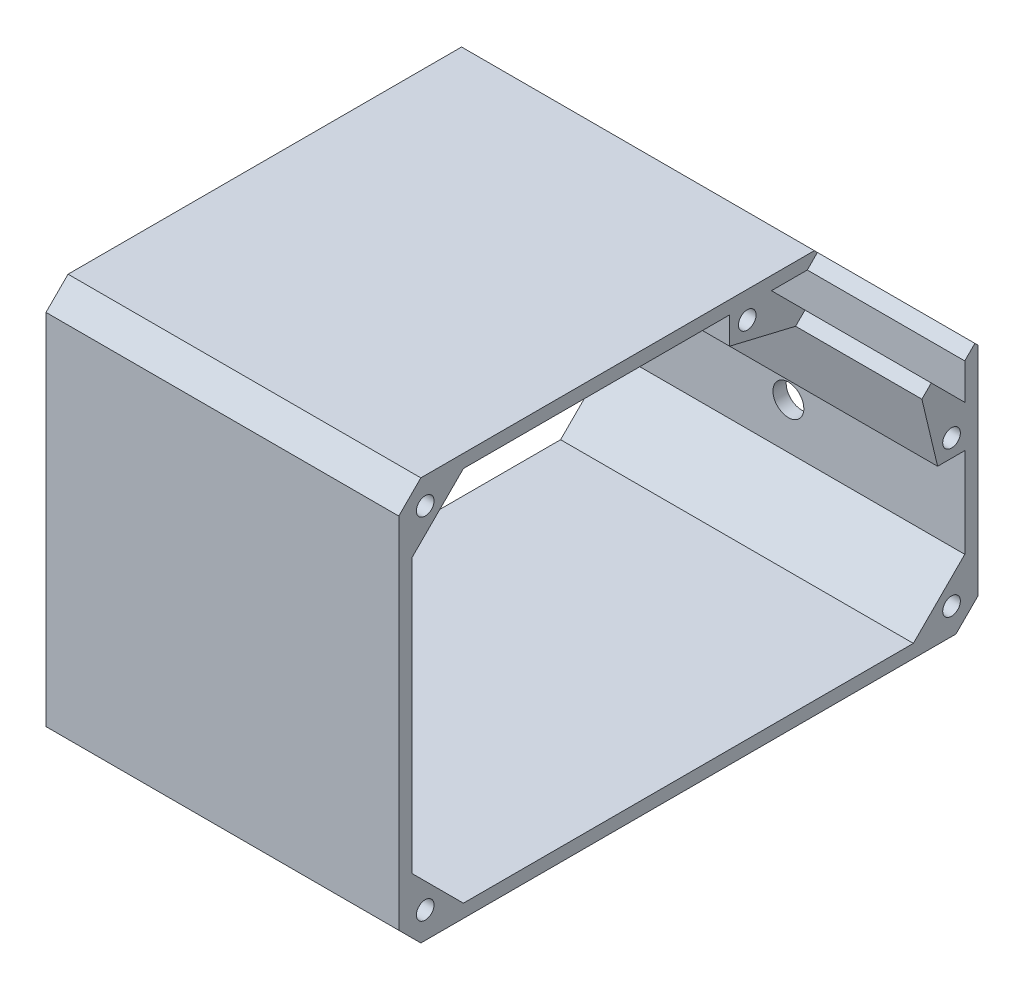
SolidWorks part; units mm, degrees
ref_plane "Front Plane" through (0, 0, 0) normal (0, 0, 1) x (1, 0, 0)
ref_plane "Top Plane" through (0, 0, 0) normal (0, 1, 0) x (1, 0, 0)
ref_plane "Right Plane" through (0, 0, 0) normal (1, 0, 0) x (0, 0, -1)
sketch "Sketch2" plane through (0, 0, 0) normal (1, 0, 0) x (0, 0, -1)
  line L1 (53.7307, 35.7377) -> (89.086, 0.3824) construction
  line L3 (89.086, -49.6176) -> (-36.2693, -49.6176)
  line L4 (-36.2693, -49.6176) -> (-36.2693, 35.7377)
  line L5 (-39.2693, -52.6176) -> (-39.2693, 38.7377)
  line L6 (-39.2693, 38.7377) -> (54.9733, 38.7377)
  line L7 (54.9733, 38.7377) -> (92.086, 1.625) construction
  line L8 (92.086, 1.625) -> (92.086, -52.6176)
  line L9 (92.086, -52.6176) -> (-39.2693, -52.6176)
  line L10 (53.7307, 35.7377) -> (55.852, 37.859) construction
  line L11 (89.086, 0.3824) -> (91.2073, 2.5037) construction
  line L12 (49.3113, 31.6718) -> (89.086, -8.1029) construction
  line L13 (53.3771, 35.7377) -> (55.6752, 38.0358)
  line L14 (55.6752, 38.0358) -> (54.9733, 38.7377)
  line L15 (91.2073, 2.5037) -> (92.086, 1.625)
  line L16 (89.086, 0.0288) -> (91.3841, 2.3269)
  line L17 (85.1969, -8.4565) -> (44.8918, 31.8486) construction
  line L18 (-36.2693, 35.7377) -> (53.3771, 35.7377)
  line L19 (-36.2693, 35.7377) -> (53.7307, 35.7377) construction
  line L20 (89.086, -49.6176) -> (89.086, 0.0288)
  line L21 (89.086, 0.3824) -> (89.086, -49.6176) construction
  line L22 (44.8918, 31.8486) -> (50.7255, 26.015)
  line L23 (50.7255, 26.015) -> (52.8468, 28.1363)
  line L24 (52.8468, 28.1363) -> (49.3113, 31.6718)
  line L25 (53.3771, 35.7377) -> (49.3113, 31.6718)
  line L26 (85.1969, -8.4565) -> (79.363, -2.6225)
  line L27 (79.363, -2.6225) -> (81.4843, -0.5012)
  line L28 (85.0198, -4.0367) -> (81.4843, -0.5012)
  line L29 (89.086, -8.1029) -> (89.086, 0.0288)
  line L30 (89.086, 0.0288) -> (85.0198, -4.0367)
  line L31 (49.3113, 31.6718) -> (45.2454, 35.7377)
  line L32 (44.8918, 31.8486) -> (51.0028, 35.7377)
  line L33 (85.1969, -8.4565) -> (89.086, -12.3456)
  line L34 (85.0198, -4.0367) -> (89.086, -8.1029)
  line L35 (-36.2693, 24.0809) -> (-24.6125, 35.7377)
  line L36 (50.7255, 26.015) -> (9.8915, 35.7377) construction
  line L37 (35.7601, 35.7377) -> (35.7601, 29.5783)
  line L38 (35.7601, 29.5783) -> (50.7255, 26.015)
  line L39 (-36.2693, -37.9608) -> (-24.6125, -49.6176)
  line L40 (73.5297, 20.1814) -> (65.0444, 11.6961) construction
  line L41 (89.086, -17.5882) -> (82.9266, -17.5882)
  line L42 (82.9266, -17.5882) -> (79.3633, -2.6228)
  line L43 (26.4084, -52.6176) -> (26.4084, 38.7377) construction
  line L44 (89.086, -37.9608) -> (77.4292, -49.6176)
  circle A0 centre (-33.2693, 32.7377) radius 2
  circle A1 centre (39.7601, 32.7377) radius 2
  circle A2 centre (-33.2693, -46.6176) radius 2
  circle A4 centre (86.086, -13.5882) radius 2
  circle A5 centre (86.086, -46.6176) radius 2
  dimension "D11" = 4
  dimension "D14" = 4
  dimension "D16" = 4
  dimension "D19" = 4
  dimension "D21" = 4
  dimension "D25" = 4
  dimension "D1" = 90
  dimension "D2" = 5
  dimension "D3" = 50
  dimension "D4" = 50
  dimension "D6" = 6
  dimension "D7" = 0.25
  dimension "D8" = 0.25
  dimension "D9" = 3
  dimension "D10" = 5
  dimension "D12" = 6
  dimension "D13" = 6
  dimension "D15" = 135
  dimension "D17" = 6
  dimension "D18" = 6
  dimension "D20" = 4
  dimension "D22" = 135
  dimension "D23" = 6
  dimension "D24" = 6
  dimension "D5" = 3
extrude "Boss-Extrude2" add sketch "Sketch2" along normal blind 80 contours L20 L3 L4 L18 L13 L14 L6 L5 L9 L8 L15 L16 | L4 L35 L18 A0 | L37 L38 L22 L32 L18 A1 | L32 L22 L23 L24 L31 L18 | L42 L41 L20 L33 L26 A4 | L34 L28 L27 L26 L33 L20 | L20 L44 L3 A5 | L39 L4 L3 A2
chamfer "Chamfer2" distance 5 angle 45 3 edges at (40, -52.6176, -92.086) (40, -52.6176, 39.2693) (40, 38.7377, 39.2693)
sketch "Sketch3" plane through (0, 0, -92.086) normal (0, 0, -1) x (-1, 0, 0)
  line L0 (-40, -47.6176) -> (-40, 1.625) construction
  line L1 (-80, -47.6176) -> (0, -47.6176) construction
  line L2 (-80, 1.625) -> (0, 1.625) construction
  circle A0 centre (-40, -27.6176) radius 3.5
  dimension "D1" = 7
  dimension "D2" = 20
extrude "Cut-Extrude1" cut sketch "Sketch3" against normal up to next
